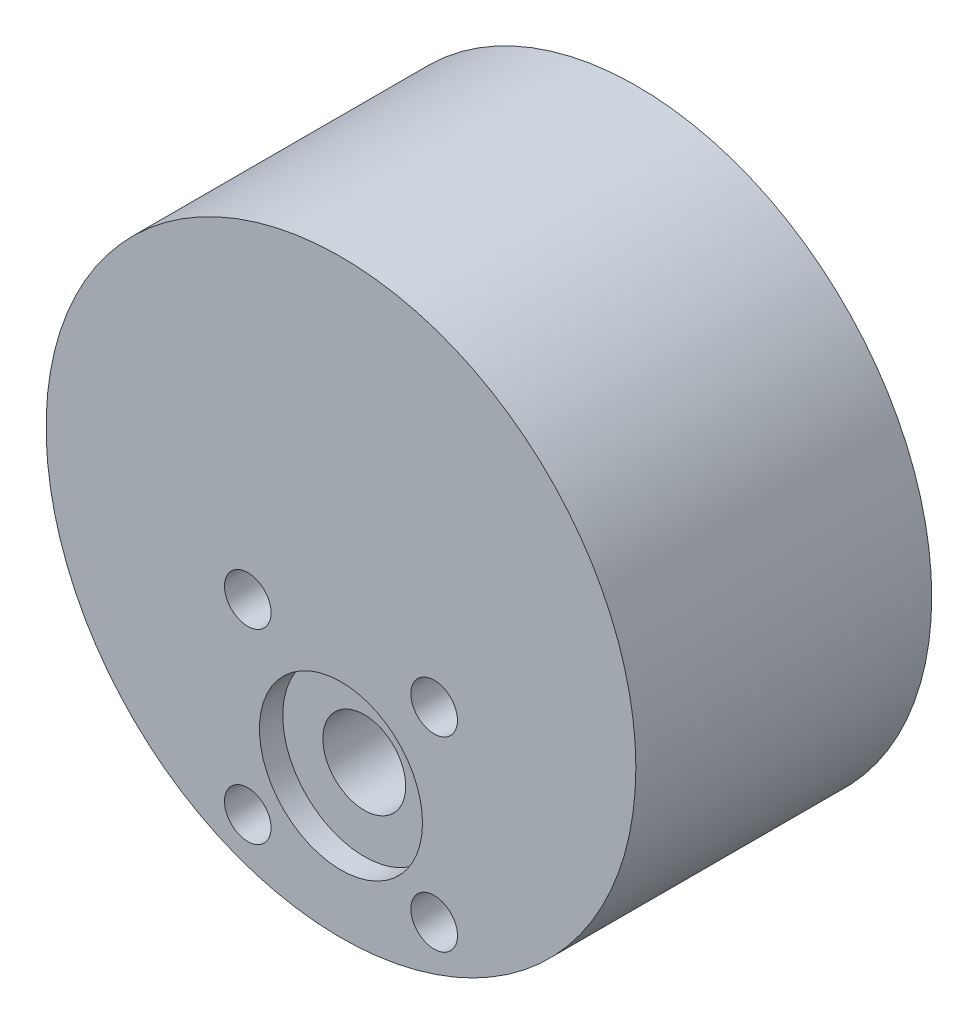
SolidWorks part; units mm, degrees
ref_plane "Front Plane" through (0, 0, 0) normal (0, 0, 1) x (1, 0, 0)
ref_plane "Top Plane" through (0, 0, 0) normal (0, 1, 0) x (1, 0, 0)
ref_plane "Right Plane" through (0, 0, 0) normal (1, 0, 0) x (0, 0, -1)
sketch "Sketch1" plane through (0, 0, 0) normal (0, 0, 1) x (1, 0, 0)
  circle A0 centre (0, 0) radius 25.3146
extrude "Boss-Extrude1" add sketch "Sketch1" along normal blind 25.4
sketch "Sketch2" plane through (0, 0, 25.4) normal (0, 0, 1) x (1, 0, 0)
  circle A0 centre (0, -13.2788) radius 3.556
  dimension "D1" = 7.112
extrude "Cut-Extrude1" cut sketch "Sketch2" against normal blind 25.4
sketch "Sketch3" plane through (0, 0, 25.4) normal (0, 0, 1) x (1, 0, 0)
  circle A0 centre (0, -13.2788) radius 7
  circle A1 centre (0, 0) radius 25.3146
  circle A2 centre (0, 0) radius 25.3146
  circle A3 centre (0, -13.2788) radius 3.175
  circle M3 centre (0, -13.2788) radius 3.556
  dimension "D2" = 14
  dimension "D1" = 0
extrude "Cut-Extrude2" cut sketch "Sketch3" against normal blind 2 contours A0 M3
sketch "Sketch4" plane through (0, 0, 25.4) normal (0, 0, 1) x (1, 0, 0)
  circle A0 centre (-8, -4.1582) radius 2
  circle A1 centre (0, 0) radius 25.3146
  circle A2 centre (0, 0) radius 25.3146
  circle A3 centre (8, -4.1582) radius 2
  circle A4 centre (8, -20.1582) radius 2
  circle A5 centre (-8, -20.1582) radius 2
  circle A7 centre (0, -13.2788) radius 3.556 construction
  dimension "D2" = 16
  dimension "D3" = 16
  dimension "D4" = 16
  dimension "D5" = 16
  dimension "D6" = 16
  dimension "D7" = 8
  dimension "D8" = 4
  dimension "D9" = 4
  dimension "D10" = 4
  dimension "D1" = 0
extrude "Cut-Extrude3" cut sketch "Sketch4" against normal through all contours A5 | A4 | A3 | A0
